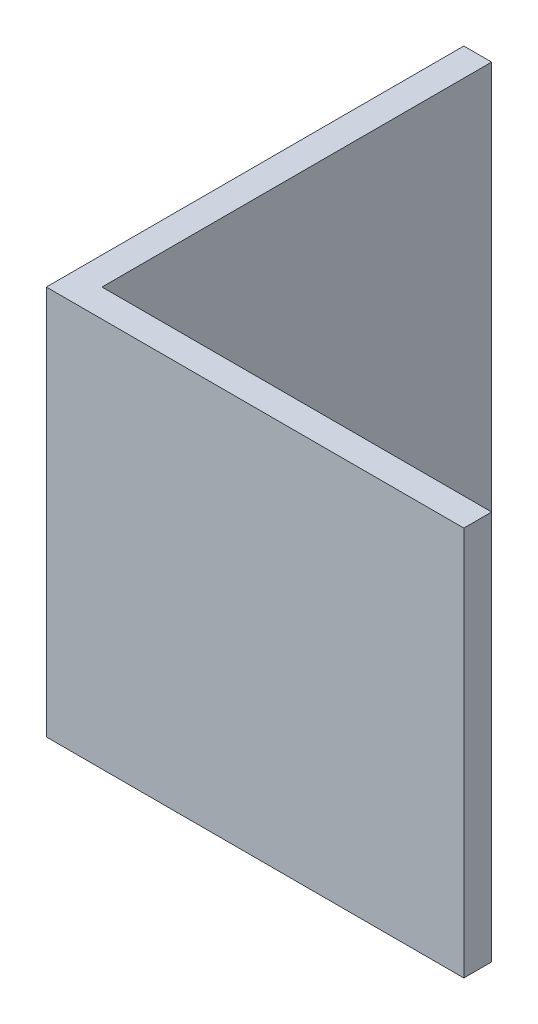
SolidWorks part; units mm, degrees
material "1060 Сплав"
ref_plane "Спереди" through (0, 0, 0) normal (0, 0, 1) x (1, 0, 0)
ref_plane "Сверху" through (0, 0, 0) normal (0, 1, 0) x (1, 0, 0)
ref_plane "Справа" through (0, 0, 0) normal (1, 0, 0) x (0, 0, -1)
sketch "Эскиз1" plane through (0, 0, 0) normal (0, 1, 0) x (1, 0, 0)
  line L0 (0, 0) -> (0, 15)
  line L1 (0, 15) -> (1, 15)
  line L2 (1, 15) -> (1, 1)
  line L3 (1, 1) -> (15, 1)
  line L4 (15, 1) -> (15, 0)
  line L5 (15, 0) -> (0, 0)
  dimension "D1" = 1
  dimension "D2" = 15
extrude "Бобышка-Вытянуть1" add sketch "Эскиз1" along normal blind 14
sketch "Эскиз2" plane through (0, 0, 0) normal (0, 0, 1) x (1, 0, 0)
  line L0 (7.5, 14) -> (7.5, 0) construction
  line L1 (0, 14) -> (15, 14) construction
  line L2 (0, 0) -> (15, 0) construction
